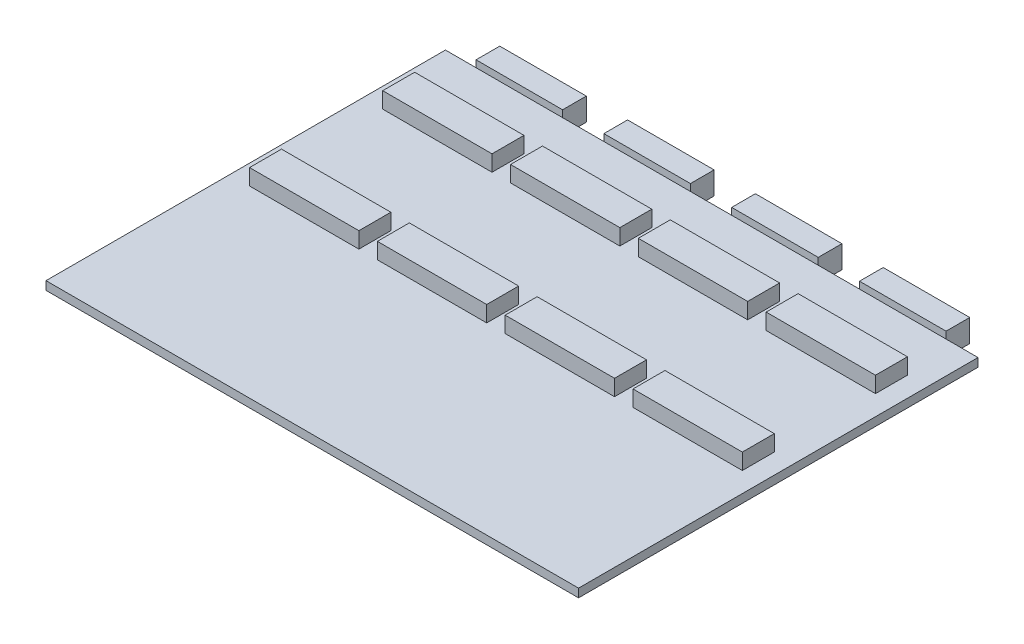
SolidWorks part; units mm, degrees
ref_plane "Front Plane" through (0, 0, 0) normal (0, 0, 1) x (1, 0, 0)
ref_plane "Top Plane" through (0, 0, 0) normal (0, 1, 0) x (1, 0, 0)
ref_plane "Right Plane" through (0, 0, 0) normal (1, 0, 0) x (0, 0, -1)
sketch "Sketch1" plane through (0, 0, 0) normal (0, 1, 0) x (1, 0, 0)
  line L1 (0, 0) -> (100, 0)
  line L2 (0, 0) -> (0, 75)
  line L3 (0, 75) -> (100, 75)
  line L4 (100, 0) -> (100, 75)
extrude "Boss-Extrude1" add sketch "Sketch1" along normal blind 1.5875
sketch "Sketch2" plane through (0, 0, 0) normal (0, 1, 0) x (1, 0, 0)
  line L1 (3.72, 40.5) -> (24.25, 40.5)
  line L2 (3.72, 40.5) -> (3.72, 34.5)
  line L3 (3.72, 34.5) -> (24.25, 34.5)
  line L4 (24.25, 40.5) -> (24.25, 34.5)
extrude "Boss-Extrude2" add sketch "Sketch2" along normal blind 4.5875
pattern_linear "LPattern1" count 4 spacing 24 along (1, 0, 0) count 2 spacing 25 along (0, 0, -1) of "Boss-Extrude2"
sketch "Sketch3" plane through (0, 0, -75) normal (0, 0, -1) x (-1, 0, 0)
  line L1 (-5.75, -1.375) -> (-22, -1.375)
  line L2 (-5.75, -1.375) -> (-5.75, 2.875)
  line L3 (-5.75, 2.875) -> (-22, 2.875)
  line L4 (-22, -1.375) -> (-22, 2.875)
extrude "Boss-Extrude3" add sketch "Sketch3" along normal blind 4.45
pattern_linear "LPattern2" count 4 spacing 24 along (1, 0, 0) of "Boss-Extrude3"
